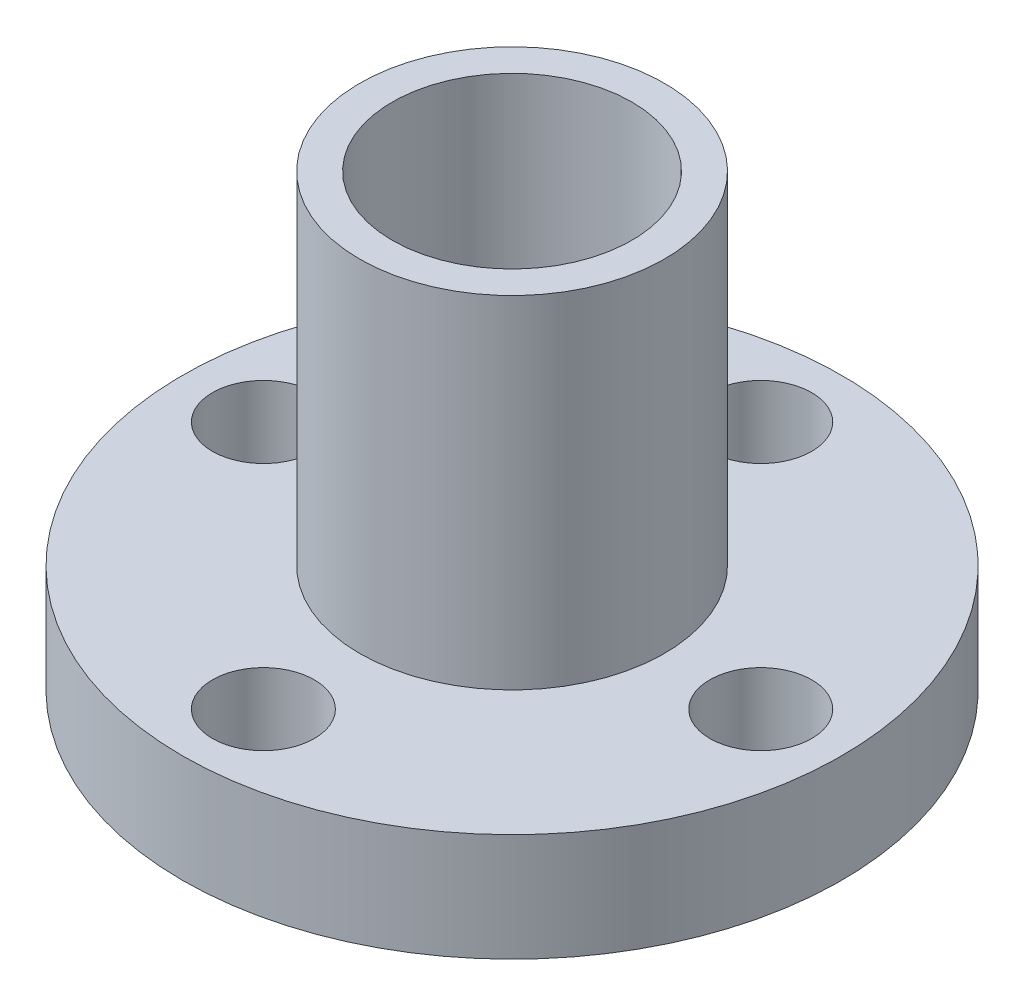
SolidWorks part; units mm, degrees
ref_plane "Front Plane" through (0, 0, 0) normal (0, 0, 1) x (1, 0, 0)
ref_plane "Top Plane" through (0, 0, 0) normal (0, 1, 0) x (1, 0, 0)
ref_plane "Right Plane" through (0, 0, 0) normal (1, 0, 0) x (0, 0, -1)
sketch "Sketch1" plane through (0, 0, 0) normal (0, 1, 0) x (1, 0, 0)
  line L0 (0, 0) -> (-8.3, 0) construction
  circle A0 centre (0, 0) radius 11
  circle A1 centre (0, 0) radius 5
  circle A2 centre (-8.3, 0) radius 1.7
  circle A3 centre (0, 8.3) radius 1.7
  circle A4 centre (8.3, 0) radius 1.7
  circle A5 centre (0, -8.3) radius 1.7
  point P15 (0, 0)
  dimension "D1" = 8.3
  dimension "D2" = 4
extrude "Boss-Extrude1" add sketch "Sketch1" along normal blind 3.6
sketch "Sketch2" plane through (0, 0, 0) normal (0, 1, 0) x (1, 0, 0)
  circle A0 centre (0, 0) radius 5.085
  circle A1 centre (0, 0) radius 4
extrude "Boss-Extrude2" add sketch "Sketch2" along normal blind 15
